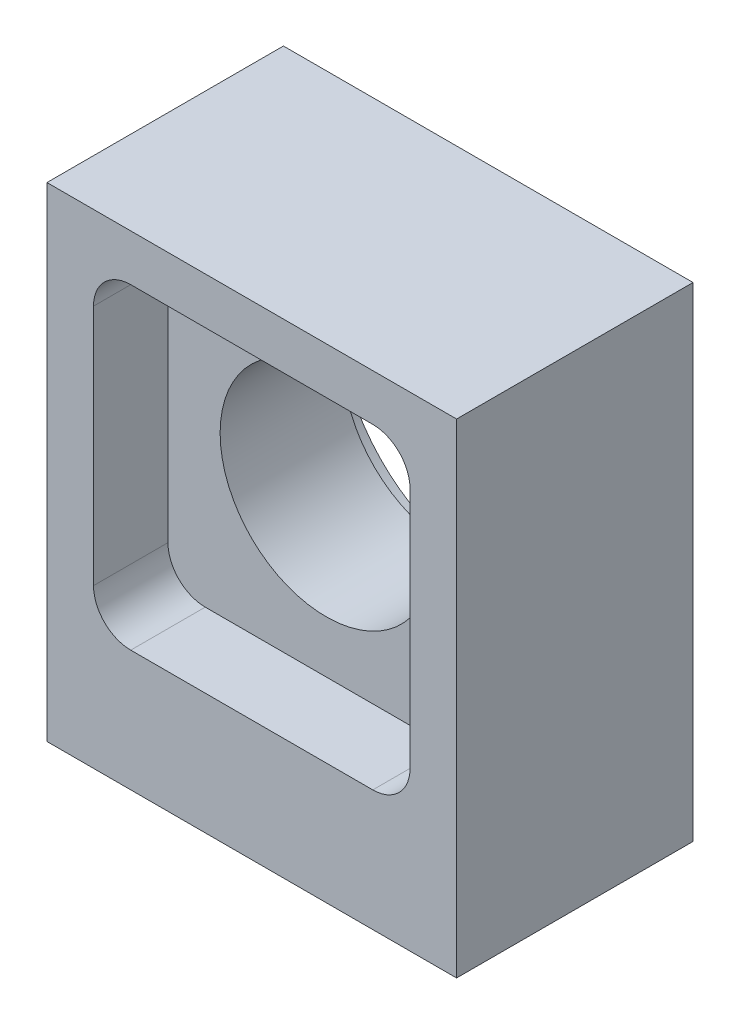
SolidWorks part; units mm, degrees
ref_plane "Front Plane" through (0, 0, 0) normal (0, 0, 1) x (1, 0, 0)
ref_plane "Top Plane" through (0, 0, 0) normal (0, 1, 0) x (1, 0, 0)
ref_plane "Right Plane" through (0, 0, 0) normal (1, 0, 0) x (0, 0, -1)
sketch "Sketch1" plane through (0, 0, 0) normal (0, 1, 0) x (1, 0, 0)
  line L1 (0, 0) -> (22, 0)
  line L2 (0, 0) -> (0, 12.7)
  line L3 (0, 12.7) -> (22, 12.7)
  line L4 (22, 0) -> (22, 12.7)
  dimension "D1" = 22
  dimension "D2" = 12.7
extrude "Boss-Extrude1" add sketch "Sketch1" along normal blind 26
hole_wizard "M3x0.5 Tapped Hole1" positions "Sketch3" profile "Sketch2" tap size "M3x0.5" standard "ANSI Metric"
sketch "Sketch3" plane through (0, 0, 0) normal (0, -1, 0) x (-1, 0, 0)
  line L0 (-22, 0) -> (-22, 12.7) construction
  line L1 (0, 0) -> (-22, 0) construction
  point P0 (-18, 3)
  dimension "D1" = 4
  dimension "D2" = 3
sketch "Sketch2" plane through (18, 0, -3) normal (1, 0, 0) x (0, 0, -1)
  line L0 (0, 0) -> (0, 5.7511)
  line L1 (0, 5.7511) -> (1.25, 5)
  line L2 (1.25, 5) -> (1.25, 0.275)
  line L3 (1.25, 0.275) -> (1.525, 0)
  line L5 (1.525, 0) -> (0, 0)
  line L6 (-1.25, 0.275) -> (-1.525, 0) construction
  line L10 (0, 5.7511) -> (-1.25, 5) construction
  line L11 (0, -6.35) -> (0, 107.95) construction
  dimension "Tap Drill Dia." = 2.5
  dimension "Tap Drill Depth" = 5
  dimension "Near C'Sink Dia." = 3.05
  dimension "Near C'Sink Angle" = 90
  dimension "Drill Angle" = 118
cosmetic thread "Hole Thread1" parameters "D1"=5, "D2"=3
ref_plane "Plane1" through (11, 0, 0) normal (1, 0, 0) x (0, 0, -1)
ref_plane "Plane2" through (0, 0, -6.35) normal (0, 0, 1) x (1, 0, 0)
mirror "Mirror1" about plane through (0, 0, -6.35) normal (0, 0, 1) of "M3x0.5 Tapped Hole1"
mirror "Mirror2" about plane through (11, 0, 0) normal (1, 0, 0) of "Mirror1", "M3x0.5 Tapped Hole1"
hole_wizard "M3x0.5 Tapped Hole2" positions "Sketch6" profile "Sketch4" tap size "M3x0.5" standard "ANSI Metric"
sketch "Sketch6" plane through (0, 0, 0) normal (0, -1, 0) x (-1, 0, 0)
  line L0 (-12.1, 6.35) -> (12.1, 6.35) construction
  line L1 (-11, 6.985) -> (-11, -6.985) construction
  point P0 (-11, 6.35)
sketch "Sketch4" plane through (11, 0, -6.35) normal (1, 0, 0) x (0, 0, -1)
  line L0 (0, 0) -> (0, 5.7511)
  line L1 (0, 5.7511) -> (1.25, 5)
  line L2 (1.25, 5) -> (1.25, 0.275)
  line L3 (1.25, 0.275) -> (1.525, 0)
  line L5 (1.525, 0) -> (0, 0)
  line L6 (-1.25, 0.275) -> (-1.525, 0) construction
  line L10 (0, 5.7511) -> (-1.25, 5) construction
  line L11 (0, -6.35) -> (0, 107.95) construction
  dimension "Tap Drill Dia." = 2.5
  dimension "Tap Drill Depth" = 5
  dimension "Near C'Sink Dia." = 3.05
  dimension "Near C'Sink Angle" = 90
  dimension "Drill Angle" = 118
cosmetic thread "Hole Thread2" parameters "D1"=5, "D2"=3
sketch "Sketch7" plane through (0, 0, 0) normal (0, 0, 1) x (1, 0, 0)
  line L0 (11, -6.985) -> (11, 6.985) construction
  line L1 (0, 0) -> (22, 0) construction
  circle A0 centre (11, 15) radius 5.7
  dimension "D1" = 11.4
  dimension "D2" = 15
extrude "Cut-Extrude1" cut sketch "Sketch7" against normal through all
sketch "Sketch8" plane through (0, 0, 0) normal (0, 0, 1) x (1, 0, 0)
  line L0 (0, 26) -> (0, 0) construction
  line L1 (2.5, 6.5) -> (19.5, 6.5)
  line L2 (2.5, 6.5) -> (2.5, 23.5)
  line L3 (2.5, 23.5) -> (19.5, 23.5)
  line L4 (19.5, 6.5) -> (19.5, 23.5)
  line L5 (0, 26) -> (22, 26) construction
  dimension "D1" = 2.5
  dimension "D2" = 2.5
  dimension "D3" = 17
  dimension "D4" = 17
extrude "Cut-Extrude2" cut sketch "Sketch8" against normal blind 4
fillet "Fillet1" radius 2 4 edges at (19.5, 6.5, -2) (2.5, 6.5, -2) (19.5, 23.5, -2) (2.5, 23.5, -2)
sketch "Sketch9" plane through (0, 0, -12.7) normal (0, 0, -1) x (-1, 0, 0)
  circle A0 centre (-11, 15) radius 8.05
  dimension "D1" = 16.1
extrude "Cut-Extrude3" cut sketch "Sketch9" against normal blind 2.1
